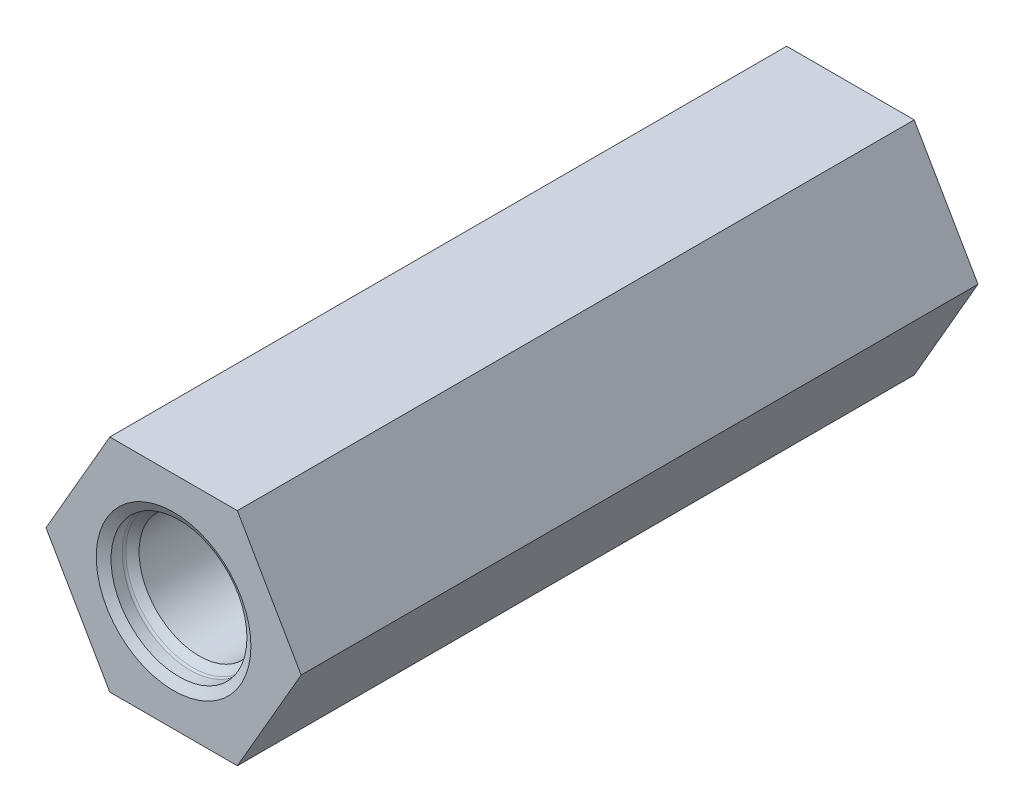
SolidWorks part; units mm, degrees
material "6061-T6 (SS)"
ref_plane "Front Plane" through (0, 0, 0) normal (0, 0, 1) x (1, 0, 0)
ref_plane "Top Plane" through (0, 0, 0) normal (0, 1, 0) x (1, 0, 0)
ref_plane "Right Plane" through (0, 0, 0) normal (1, 0, 0) x (0, 0, -1)
sketch "Sketch1" plane through (0, 0, 0) normal (0, 0, 1) x (1, 0, 0)
  line L1 (-18.3309, 0) -> (-9.1654, -15.875)
  line L2 (-9.1654, -15.875) -> (9.1654, -15.875)
  line L3 (9.1654, -15.875) -> (18.3309, 0)
  line L4 (18.3309, 0) -> (9.1654, 15.875)
  line L5 (9.1654, 15.875) -> (-9.1654, 15.875)
  line L6 (-9.1654, 15.875) -> (-18.3309, 0)
  circle A0 centre (0, 0) radius 15.875 construction
  dimension "D1" = 31.75
extrude "Extrude1" add sketch "Sketch1" along normal blind 97.2598
sketch "Sketch3" plane through (0, 0, 97.2598) normal (0, 0, 1) x (1, 0, 0)
  circle A0 centre (0, 0) radius 5.3581
  dimension "D1" = 10.7163
extrude "Cut-Extrude3" cut sketch "Sketch3" against normal through all
sketch "Sketch4" plane through (-13.7482, -7.9375, 0) normal (-0.866, -0.5, 0) x (0, 0, 1)
  line L0 (0, 9.1654) -> (0, -9.1654) construction
  circle A0 centre (21.59, 0) radius 4.2164
  point P2 (0, 0)
  dimension "D2" = 8.4328
  dimension "D1" = 21.59
extrude "Cut-Extrude2" cut sketch "Sketch4" against normal up to next
sketch "Sketch5" plane through (0, 0, 0) normal (0, 0, -1) x (-1, 0, 0)
  circle A0 centre (0, 0) radius 6.3754
  dimension "D1" = 12.7508
extrude "Cut-Extrude4" cut sketch "Sketch5" against normal blind 26.162
cosmetic thread "Cosmetic Thread1" parameters "D1"=15.1892, "D2"=14.2875
sketch "Sketch6" plane through (0, 0, 97.2598) normal (0, 0, 1) x (1, 0, 0)
  circle A0 centre (0, 0) radius 7.1438
  dimension "D1" = 14.2875
extrude "Cut-Extrude5" cut sketch "Sketch6" against normal blind 63.5
sketch "Sketch8" plane through (0, 0, 0) normal (0, 1, 0) x (1, 0, 0)
  line L0 (0, -97.2598) -> (0, -76.0762)
  line L1 (9.1654, -97.2598) -> (-9.1654, -97.2598) construction
  line L2 (0, -76.0762) -> (-6.1468, -76.0762)
  line L3 (-6.1468, -76.0762) -> (-8.6614, -78.2098)
  line L4 (-8.6614, -78.2098) -> (-8.6614, -93.5569)
  line L5 (0, -97.2598) -> (-11.1125, -97.2598)
  line L6 (-11.1125, -97.2598) -> (-9.7663, -96.4825)
  line L7 (-9.7663, -96.4825) -> (-9.7663, -94.8722)
  line L8 (-9.6175, -94.513) -> (-8.6614, -93.5569)
  arc A0 (-9.6175, -94.513) -> (-9.7663, -94.8722) centre (-9.2583, -94.8722) ccw
  dimension "D5" = 0.508
  dimension "D1" = 11.1125
  dimension "D2" = 60
  dimension "D3" = 6.1468
  dimension "D4" = 9.7663
  dimension "D6" = 2.3876
  dimension "D7" = 45
  dimension "D8" = 19.05
  dimension "D9" = 21.1836
  dimension "D10" = 8.6614
revolve "Cut-Revolve1" cut sketch "Sketch8" angle 360 about L0
cosmetic thread "Cosmetic Thread2" parameters "D1"=18.1356, "D2"=19.05
thread "Thread1" pitch 1.5875 start angle 0, offset 0, length 12.7, pitch 1.5875, diameter 16.9004
ref_plane "Plane1" through (-8.4502, 0, 93.3456) normal (0, -1, 0) x (-1, 0, 0)
sketch "Thread Profile1" plane through (-8.4502, 0, 93.3456) normal (0, -1, 0) x (-1, 0, 0)
  line L0 (0, 0) -> (0, 1.5875) construction
  line L1 (0, 0) -> (0.8593, 0.4961)
  line L2 (0.8593, 0.4961) -> (0.8593, 0.6945)
  line L3 (0.8593, 0.6945) -> (0, 1.1906)
  line L4 (0.8593, 0.5953) -> (0, 0.5953) construction
  line L11 (0, 0) -> (0, 1.1906)
  point P2 (0, 0)
  dimension "Pitch" = 1.5875
  dimension "Profile_Angle" = 60
  dimension "Profile_Land" = 0.1984
  dimension "Profile_Height" = 0.8593
sketch "Sketch10" plane through (0, 0, 0) normal (0, 1, 0) x (1, 0, 0)
  line L0 (0, 0) -> (-8.7376, 0)
  line L1 (-8.7376, 0) -> (-7.366, -0.7919)
  line L2 (-7.366, -0.7919) -> (-7.366, -2.1082)
  line L3 (-7.2172, -2.4674) -> (-6.3754, -3.3092)
  line L5 (0, 0) -> (0, 9.6548) construction
  line L6 (-6.3754, -3.3092) -> (-6.3754, -17.907)
  line L7 (-6.3754, -17.907) -> (0, -17.907)
  line L8 (0, -17.907) -> (0, 0)
  arc A0 (-7.2172, -2.4674) -> (-7.366, -2.1082) centre (-6.858, -2.1082) cw
  dimension "D4" = 0.508
  dimension "D1" = 8.7376
  dimension "D2" = 7.366
  dimension "D3" = 60
  dimension "D5" = 2.1082
  dimension "D6" = 45
  dimension "D7" = 6.3754
  dimension "D8" = 17.907
revolve "Cut-Revolve2" cut sketch "Sketch10" angle 360 about L5
thread "Thread2" pitch 1.4111 start angle 0, offset 0, length 12.1412, pitch 1.4111, diameter 12.7508
ref_plane "Plane2" through (6.3754, 0, 3.3092) normal (0, -1, 0) x (1, 0, 0)
sketch "Thread Profile2" plane through (6.3754, 0, 3.3092) normal (0, -1, 0) x (1, 0, 0)
  line L0 (0, 0) -> (0, 1.4111) construction
  line L1 (0, 0) -> (0.7638, 0.441)
  line L2 (0.7638, 0.441) -> (0.7638, 0.6174)
  line L3 (0.7638, 0.6174) -> (0, 1.0583)
  line L4 (0.7638, 0.5292) -> (0, 0.5292) construction
  line L11 (0, 0) -> (0, 1.0583)
  point P2 (0, 0)
  dimension "Pitch" = 1.4111
  dimension "Profile_Angle" = 60
  dimension "Profile_Land" = 0.1764
  dimension "Profile_Height" = 0.7638
